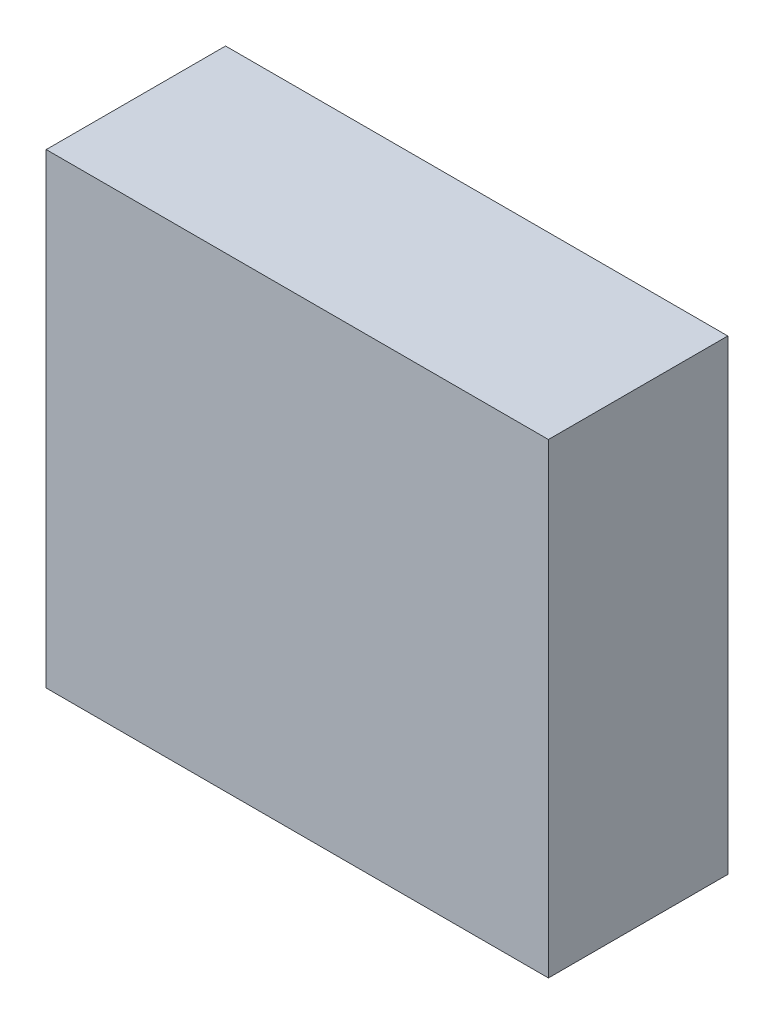
SolidWorks part; units mm, degrees
ref_plane "前视基准面" through (0, 0, 0) normal (0, 0, 1) x (1, 0, 0)
ref_plane "上视基准面" through (0, 0, 0) normal (0, 1, 0) x (1, 0, 0)
ref_plane "右视基准面" through (0, 0, 0) normal (1, 0, 0) x (0, 0, -1)
other "Configuration Table"
sketch "草图1" plane through (0, 0, 0) normal (0, 0, 1) x (1, 0, 0)
  line L1 (-35, 32.5) -> (35, 32.5)
  line L2 (-35, 32.5) -> (-35, -32.5)
  line L3 (-35, -32.5) -> (35, -32.5)
  line L4 (35, 32.5) -> (35, -32.5)
  line L5 (-35, 32.5) -> (35, -32.5) construction
  line L6 (-35, -32.5) -> (35, 32.5) construction
  point P0 (0, 0)
  dimension "D1" = 65
  dimension "D2" = 70
extrude "凸台-拉伸1" add sketch "草图1" along normal blind 25
